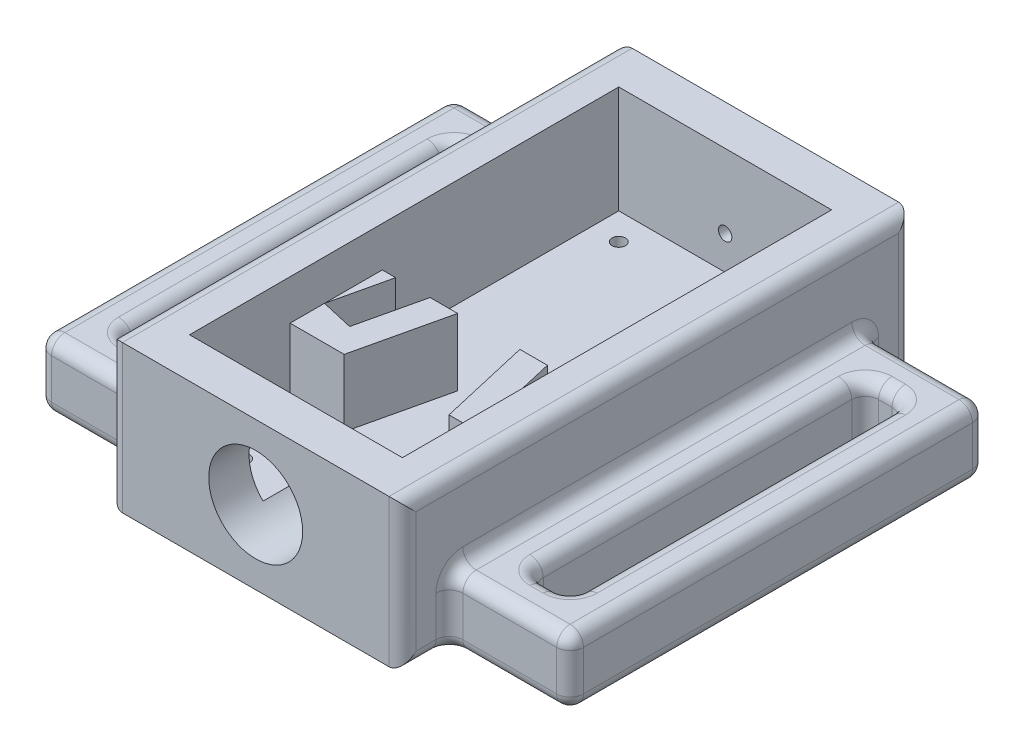
SolidWorks part; units mm, degrees
ref_plane "Front Plane" through (0, 0, 0) normal (0, 0, 1) x (1, 0, 0)
ref_plane "Top Plane" through (0, 0, 0) normal (0, 1, 0) x (1, 0, 0)
ref_plane "Right Plane" through (0, 0, 0) normal (1, 0, 0) x (0, 0, -1)
sketch "Sketch1" plane through (0, 0, 0) normal (0, 1, 0) x (1, 0, 0)
  line L1 (0, 0) -> (21.8718, 0)
  line L2 (0, 0) -> (0, 38)
  line L3 (0, 38) -> (21.8718, 38)
  line L4 (21.8718, 0) -> (21.8718, 38)
extrude "Boss-Extrude2" add sketch "Sketch1" along normal blind 11 contours L3 L4 L1 L2
sketch "Sketch2" plane through (0, 11, 0) normal (0, 1, 0) x (1, 0, 0)
  line L0 (0, 38) -> (21.8718, 38) construction
  line L1 (3, 3) -> (18.8718, 3)
  line L2 (3, 3) -> (3, 35)
  line L3 (3, 35) -> (18.8718, 35)
  line L4 (18.8718, 3) -> (18.8718, 35)
  line L6 (0, 0) -> (21.8718, 0) construction
  line L7 (0, 0) -> (0, 38) construction
  line L8 (21.8718, 0) -> (21.8718, 38) construction
  dimension "D1" = 3
  dimension "D2" = 3
  dimension "D3" = 3
  dimension "D4" = 3
extrude "Cut-Extrude1" cut sketch "Sketch2" against normal blind 8
sketch "Sketch3" plane through (0, 3, 0) normal (0, 1, 0) x (1, 0, 0)
  line L0 (5.4378, 12.5) -> (9.9368, 31.9874)
  line L1 (16.4359, 12.5) -> (11.9368, 31.9874)
  line L2 (0, 0) -> (0, 38) construction
  line L29 (0.3577, 10.5) -> (7.0287, 10.5)
  line L30 (14.845, 10.5) -> (21.516, 10.5)
  line L31 (1.9442, 17.3719) -> (8.6152, 17.3719)
  line L32 (13.2585, 17.3719) -> (19.9295, 17.3719)
  line L33 (1.9442, 17.3719) -> (0.3577, 10.5)
  line L34 (8.6152, 17.3719) -> (7.0287, 10.5)
  line L35 (3.9968, 17.3719) -> (3.0019, 13.0624)
  line L36 (3.0019, 13.0624) -> (5.4378, 12.5)
  line L37 (5.4378, 12.5) -> (6.5626, 17.3719)
  line L38 (13.2585, 17.3719) -> (14.845, 10.5)
  line L39 (19.9295, 17.3719) -> (21.516, 10.5)
  line L40 (17.8769, 17.3719) -> (18.8718, 13.0624)
  line L41 (18.8718, 13.0624) -> (16.4359, 12.5)
  line L42 (16.4359, 12.5) -> (15.3111, 17.3719)
  line L58 (18.8718, 3) -> (18.8718, 35) construction
  line L59 (3.0019, 13.0624) -> (7.5009, 32.5498)
  line L62 (3, 3) -> (18.8718, 3) construction
  line M1 (3, 35) -> (3, 3)
  line M3 (18.8718, 3) -> (18.8718, 35)
  dimension "D1" = 20
  dimension "D2" = 20
  dimension "D6" = 20
  dimension "D7" = 5
  dimension "D8" = 2
  dimension "D9" = 2
  dimension "D10" = 5.4378
  dimension "D36" = 77
  dimension "D37" = 2
  dimension "D38" = 2
  dimension "D39" = 2.5
  dimension "D40" = 2.5
  dimension "D41" = 2
  dimension "D44" = 77
  dimension "D45" = 5
  dimension "D47" = 2
  dimension "D50" = 7.5
extrude "Boss-Extrude4" add sketch "Sketch3" along normal blind 5 contours L41 L42 L32 L38 L30 M3 | L35 L31 M1 | L32 L40 M3
sketch "Sketch4" plane through (0, 0, 0) normal (0, 0, 1) x (1, 0, 0)
  line L0 (0, 11) -> (21.8718, 11) construction
  line L1 (21.8718, 11) -> (21.8718, 0) construction
  circle A0 centre (10.9318, 5.5) radius 3.5
  dimension "D1" = 5.5
  dimension "D2" = 10.94
extrude "Cut-Extrude2" cut sketch "Sketch4" against normal blind 10
sketch "Sketch9" plane through (0, 0, -38) normal (0, 0, 1) x (1, 0, 0)
  circle A0 centre (10.9318, 5.5) radius 3.5
extrude "Cut-Extrude3" cut sketch "Sketch9" along normal blind 1.5
sketch "Sketch8" plane through (0, 0, 0) normal (0, 1, 0) x (1, 0, 0)
  line L0 (0, 0) -> (0, 38) construction
  line L1 (0, 3.5) -> (-8.7888, 3.5)
  line L2 (0, 3.5) -> (0, 34.5)
  line L3 (0, 34.5) -> (-8.7888, 34.5)
  line L4 (-8.7888, 3.5) -> (-8.7888, 34.5)
  line L5 (21.8718, 0) -> (21.8718, 38) construction
  line L6 (-5.7888, 31.5) -> (-3, 31.5)
  line L7 (-5.7888, 31.5) -> (-5.7888, 6.5)
  line L8 (-5.7888, 6.5) -> (-3, 6.5)
  line L9 (-3, 31.5) -> (-3, 6.5)
  line L10 (21.8718, 3.5) -> (30.8718, 3.5)
  line L11 (21.8718, 3.5) -> (21.8718, 34.5)
  line L12 (21.8718, 34.5) -> (30.8718, 34.5)
  line L13 (30.8718, 3.5) -> (30.8718, 34.5)
  line L15 (24.8718, 31.5) -> (27.8718, 31.5)
  line L16 (24.8718, 31.5) -> (24.8718, 6.5)
  line L17 (24.8718, 6.5) -> (27.8718, 6.5)
  line L18 (27.8718, 31.5) -> (27.8718, 6.5)
  dimension "D1" = 25
  dimension "D2" = 3
  dimension "D3" = 3
  dimension "D4" = 3
  dimension "D5" = 3
  dimension "D6" = 3
  dimension "D7" = 3
  dimension "D8" = 3
  dimension "D9" = 3
  dimension "D10" = 25
  dimension "D11" = 3
  dimension "D12" = 3.5
  dimension "D13" = 3.5
  dimension "D14" = 3.5
extrude "Boss-Extrude5" add sketch "Sketch8" along normal blind 5
fillet "Fillet1" radius 1 56 edges at (-4.3944, 5, -3.5) (21.8718, 5.5, 0) (21.8718, 11, -19) (21.8718, 5.5, -38) (26.3718, 0, -31.5) (26.3718, 5, -31.5) (26.3718, 0, -6.5) (26.3718, 5, -6.5) (27.8718, 2.5, -31.5) (27.8718, 2.5, -6.5) (27.8718, 0, -19) (27.8718, 5, -19) (26.3718, 5, -34.5) (24.8718, 2.5, -6.5) (24.8718, 2.5, -31.5) (24.8718, 0, -19) (24.8718, 5, -19) (0, 5.5, -38) (0, 11, -19) (0, 5.5, 0) (-4.3944, 5, -34.5) (-8.7888, 2.5, -34.5) (-8.7888, 2.5, -3.5) (-8.7888, 0, -19) (-8.7888, 5, -19) (-4.3944, 0, -31.5) (-4.3944, 5, -31.5) (-5.7888, 2.5, -31.5) (-5.7888, 0, -19) (-5.7888, 5, -19) (-5.7888, 2.5, -6.5) (-4.3944, 0, -6.5) (-4.3944, 5, -6.5) (-3, 2.5, -31.5) (-3, 2.5, -6.5) (-3, 0, -19) (-3, 5, -19) (0, 5, -19) (26.3718, 5, -3.5) (30.8718, 2.5, -3.5) (30.8718, 2.5, -34.5) (30.8718, 0, -19) (30.8718, 5, -19) (21.8718, 5, -19)
sketch "Sketch10" plane through (0, 0, -36.5) normal (0, 0, -1) x (-1, 0, 0)
  line L0 (-21.8718, 1) -> (-21.8718, 10) construction
  line L1 (-1, 11) -> (-20.8718, 11) construction
  circle A0 centre (-10.9318, 5.5) radius 0.5
  dimension "D1" = 10.94
  dimension "D2" = 5.5
extrude "Cut-Extrude4" cut sketch "Sketch10" against normal blind 1.5
sketch "Sketch11" plane through (0, 3, 0) normal (0, 1, 0) x (1, 0, 0)
  line L1 (18.8718, 35) -> (3, 35) construction
  line L2 (3, 35) -> (3, 3) construction
  line L3 (18.8718, 3) -> (18.8718, 35) construction
  line L4 (18.8718, 3) -> (18.8718, 10.5) construction
  line L5 (3, 3) -> (8.4823, 3) construction
  line L6 (13.3813, 3) -> (18.8718, 3) construction
  circle A0 centre (5, 33) radius 0.5
  circle A1 centre (16.8718, 33) radius 0.5
  circle A2 centre (5, 5) radius 0.5
  circle A3 centre (16.8718, 5) radius 0.5
  dimension "D1" = 2
  dimension "D3" = 2
  dimension "D5" = 2
  dimension "D6" = 2
  dimension "D7" = 2
  dimension "D8" = 2
  dimension "D2" = 2
  dimension "D4" = 2
extrude "Cut-Extrude5" cut sketch "Sketch11" against normal blind 3
